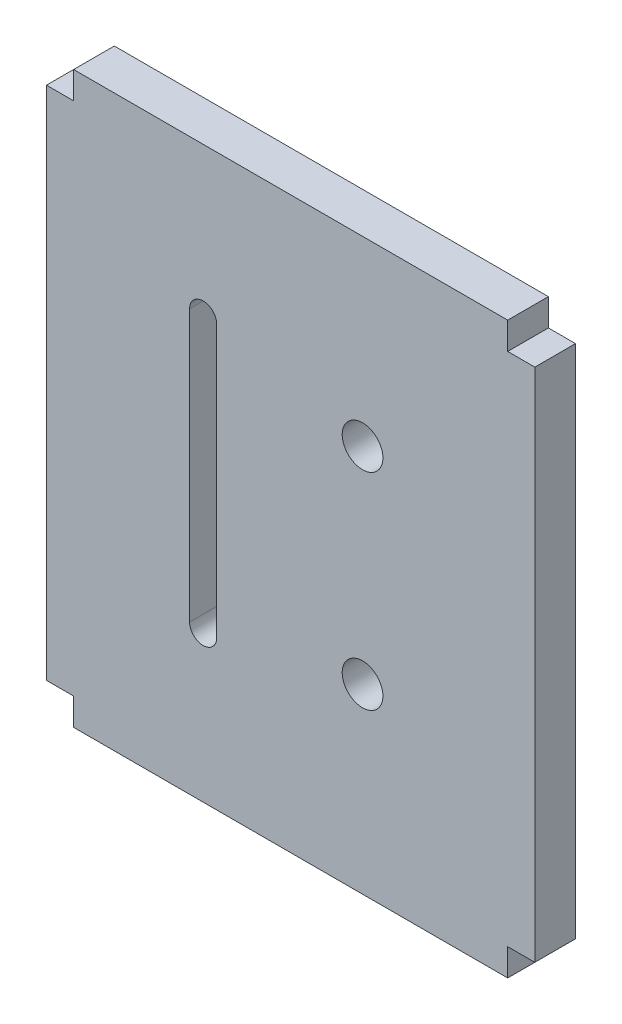
SolidWorks part; units mm, degrees
ref_plane "前视基准面" through (0, 0, 0) normal (0, 0, 1) x (1, 0, 0)
ref_plane "上视基准面" through (0, 0, 0) normal (0, 1, 0) x (1, 0, 0)
ref_plane "右视基准面" through (0, 0, 0) normal (1, 0, 0) x (0, 0, -1)
sketch "草图1" plane through (0, 0, 0) normal (0, 0, 1) x (1, 0, 0)
  line L0 (0, 42.2662) -> (0, -31.4252) construction
  line L1 (16, -21) -> (-16, -21)
  line L2 (16, -21) -> (16, 21)
  line L3 (16, 21) -> (-16, 21)
  line L4 (-16, -21) -> (-16, 21)
  line L5 (16, -21) -> (-16, 21) construction
  line L6 (16, 21) -> (-16, -21) construction
  line L7 (-16, 19) -> (-18, 19)
  line L8 (-16, 19) -> (-16, -19)
  line L9 (-16, -19) -> (-18, -19)
  line L10 (-18, 19) -> (-18, -19)
  line L11 (-47.7492, 0) -> (31.8333, 0) construction
  line L13 (16, 19) -> (18, 19)
  line L14 (16, 19) -> (16, -19)
  line L15 (16, -19) -> (18, -19)
  line L16 (18, 19) -> (18, -19)
  point P0 (0, 0)
  dimension "D1" = 32
  dimension "D2" = 42
  dimension "D3" = 2
  dimension "D4" = 38
  dimension "D5" = 2
extrude "凸台-拉伸1" add sketch "草图1" along normal blind 3 contours L4 L1 L2 L3 | L7 L10 L9 L4 | L16 L13 L2 L15
sketch "草图2" plane through (0, 0, 3) normal (0, 0, 1) x (1, 0, 0)
  line L0 (-6.45, -10) -> (-6.45, 10) construction
  line L1 (-7.45, -10) -> (-7.45, 10)
  line L2 (-5.45, -10) -> (-5.45, 10)
  line L3 (18, 19) -> (18, -19) construction
  line L4 (16, -21) -> (-16, -21) construction
  circle A0 centre (5.3, -7.6) radius 1.5
  circle A1 centre (5.3, 7.6) radius 1.5
  arc A2 (-7.45, -10) -> (-5.45, -10) centre (-6.45, -10) ccw
  arc A3 (-5.45, 10) -> (-7.45, 10) centre (-6.45, 10) ccw
  point P6 (-6.45, 0)
  point P15 (0, 0)
  dimension "D1" = 3
  dimension "D2" = 3
  dimension "D5" = 1
  dimension "D7" = 12.7
  dimension "D8" = 13.4
  dimension "D9" = 12.7
  dimension "D3" = 15.2
  dimension "D4" = 11.75
  dimension "D6" = 20
extrude "切除-拉伸1" cut sketch "草图2" against normal blind 10
